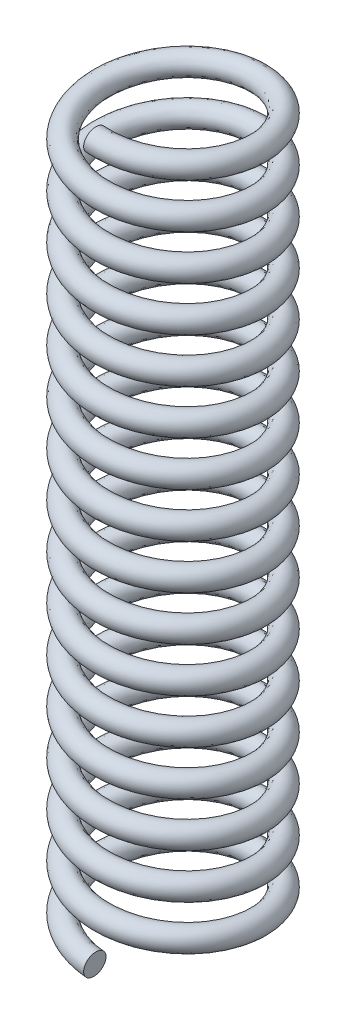
SolidWorks part; units mm, degrees
ref_plane "Front" through (0, 0, 0) normal (0, 0, 1) x (1, 0, 0)
ref_plane "Top" through (0, 0, 0) normal (0, 1, 0) x (1, 0, 0)
ref_plane "Right" through (0, 0, 0) normal (1, 0, 0) x (0, 0, -1)
sketch "Sketch1" plane through (0, 0, 0) normal (0, 1, 0) x (1, 0, 0)
  circle A0 centre (0, 0) radius 3.5
  dimension "D1" = 7
curve "Helix/Spiral1" pitch 2 height 32 turns 16
ref_plane "Plane1" through (0, 0, 3.5) normal (-0.9959, 0.0906, 0) x (0, 0, 1)
sketch "Sketch2" plane through (0, 0, 3.5) normal (-0.9959, 0.0906, 0) x (0, 0, 1)
  circle A0 centre (0, 0) radius 0.5
  dimension "D1" = 1
sweep "Sweep1" add profiles "Sketch2" path "Helix/Spiral1"
ref_plane "Plane2" through (0, 32, 0) normal (0, 1, 0) x (-1, 0, 0)
sketch "Sketch3" plane through (0, 32, 0) normal (0, 1, 0) x (-1, 0, 0)
  circle A0 centre (0, 0) radius 3.5
  circle A1 centre (0, 0) radius 3.5 construction
